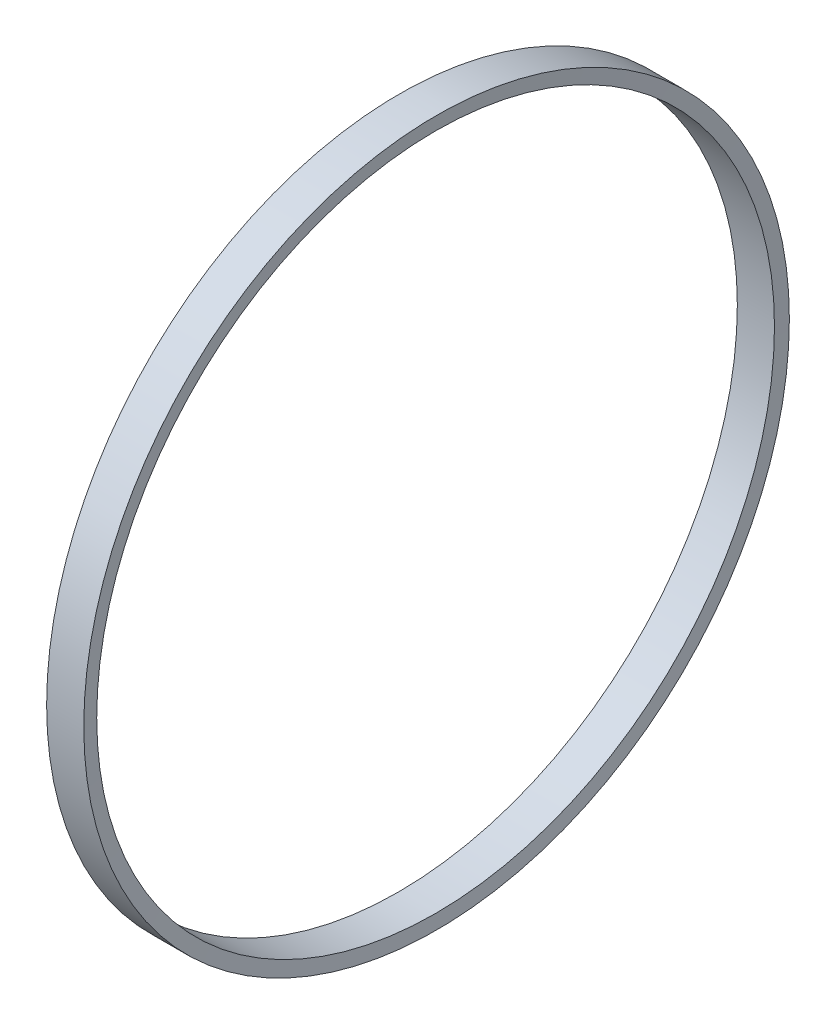
SolidWorks part; units mm, degrees
material "POLYURETHANE (11671)"
ref_plane "Přední rovina" through (0, 0, 0) normal (0, 0, 1) x (1, 0, 0)
ref_plane "Horní rovina" through (0, 0, 0) normal (0, 1, 0) x (1, 0, 0)
ref_plane "Pravá rovina" through (0, 0, 0) normal (1, 0, 0) x (0, 0, -1)
sketch "Skica2" plane through (0, 0, 0) normal (0, 0, 1) x (1, 0, 0)
  line L0 (-15.6789, 38) -> (-19.6789, 38)
  line L1 (-19.6789, 38) -> (-19.7838, 36.5)
  line L2 (-19.7838, 36.5) -> (-15.7838, 36.5)
  line L3 (-15.7838, 36.5) -> (-15.6789, 38)
  line L4 (0, 0) -> (-59.3569, 0) construction
  arc A0 (-15.7133, 37.5) -> (-15.7133, -37.5) centre (509.65, 0) ccw construction
  dimension "D1" = 1.5
  dimension "D2" = 4
  dimension "D3" = 94
  dimension "D4" = 76
revolve "Rotovat1" add sketch "Skica2" angle 360 about L4
